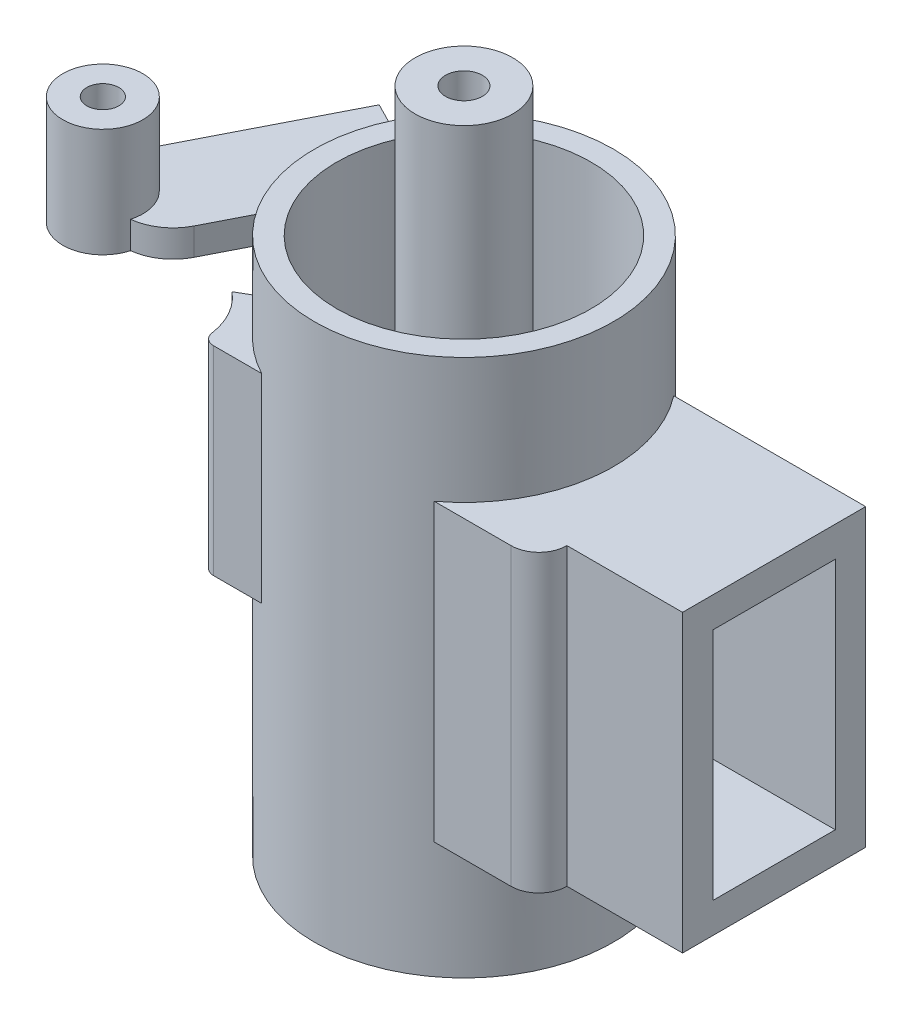
SolidWorks part; units mm, degrees
ref_plane "Front Plane" through (0, 0, 0) normal (0, 0, 1) x (1, 0, 0)
ref_plane "Top Plane" through (0, 0, 0) normal (0, 1, 0) x (1, 0, 0)
ref_plane "Right Plane" through (0, 0, 0) normal (1, 0, 0) x (0, 0, -1)
sketch "Sketch1" plane through (0, 0, 0) normal (0, 1, 0) x (1, 0, 0)
  circle A0 centre (0, 0) radius 9.35
  circle A1 centre (0, 0) radius 7.95
  dimension "D1" = 18.7
  dimension "D2" = 15.9
extrude "Boss-Extrude1" add sketch "Sketch1" along normal blind 31.6
ref_plane "Plane1" through (0, -3.3, 0) normal (0, 1, 0) x (1, 0, 0)
sketch "Sketch2" plane through (0, -3.3, 0) normal (0, 1, 0) x (1, 0, 0)
  circle A0 centre (0, 0) radius 3.05
  circle A1 centre (0, 0) radius 1.15
  dimension "D1" = 6.1
  dimension "D2" = 2.3
extrude "Boss-Extrude2" add sketch "Sketch2" along normal blind 45 separate body
ref_plane "Plane2" through (0, 7.3, 0) normal (0, 1, 0) x (1, 0, 0)
sketch "Sketch4" plane through (0, 7.3, 0) normal (0, 1, 0) x (1, 0, 0)
  line L0 (7.3924, 5.725) -> (19.3924, 5.725)
  line L1 (19.3924, 5.725) -> (19.3924, -5.725)
  line L2 (19.3924, -5.725) -> (11.6224, -5.725)
  line L4 (10.4167, -7.475) -> (5.6167, -7.475)
  circle A0 centre (0, 0) radius 9.35 construction
  arc A1 (10.4167, -7.475) -> (12.1667, -5.725) centre (10.4167, -5.725) ccw
  arc A2 (5.6167, -7.475) -> (7.3924, 5.725) centre (0, 0) ccw
  dimension "D6" = 1.75
  dimension "D1" = 5.725
  dimension "D2" = 5.725
  dimension "D3" = 12
  dimension "D4" = 4.8
  dimension "D5" = 7.77
extrude "Boss-Extrude3" add sketch "Sketch4" along normal blind 18.45
sketch "Sketch5" plane through (19.3924, 0, 0) normal (1, 0, 0) x (0, 0, -1)
  line L0 (3.825, 23.85) -> (-3.825, 23.85)
  line L1 (-3.825, 23.85) -> (-3.825, 9.2)
  line L2 (-3.825, 9.2) -> (3.825, 9.2)
  line L3 (3.825, 9.2) -> (3.825, 23.85)
  line L12 (5.725, 25.75) -> (-7.475, 25.75) construction
  line L13 (5.725, 7.3) -> (-5.725, 7.3) construction
  line L14 (-5.725, 25.75) -> (-5.725, 7.3) construction
  line L15 (5.725, 25.75) -> (5.725, 7.3) construction
  dimension "D1" = 1.9
  dimension "D2" = 1.9
  dimension "D3" = 1.9
  dimension "D4" = 1.9
extrude "Cut-Extrude1" cut sketch "Sketch5" against normal blind 15
ref_plane "Plane3" through (0, 16, 0) normal (0, 1, 0) x (1, 0, 0)
sketch "Sketch6" plane through (0, 16, 0) normal (0, 1, 0) x (1, 0, 0)
  circle A0 centre (0, 0) radius 3.05 construction
  circle A1 centre (0, 0) radius 7.95 construction
  circle A2 centre (0, 0) radius 3.05
  circle A3 centre (0, 0) radius 7.95
extrude "Boss-Extrude4" add sketch "Sketch6" along normal blind 0.2
sketch "Sketch7" plane through (0, 16, 0) normal (0, 1, 0) x (1, 0, 0)
  line L0 (6.9694, 3.825) -> (1.0694, 3.825)
  line L1 (1.0694, 3.825) -> (1.0694, 2.8564)
  line L2 (6.9694, -3.825) -> (1.0694, -3.825)
  line L3 (1.0694, -3.825) -> (1.0694, -2.8564)
  circle A0 centre (0, 0) radius 3.05 construction
  arc A2 (1.0694, -2.8564) -> (1.0694, 2.8564) centre (0, 0) ccw
  arc A4 (6.9694, -3.825) -> (6.9694, 3.825) centre (0, 0) ccw construction
  arc A5 (6.9694, -3.825) -> (6.9694, 3.825) centre (0, 0) ccw
  dimension "D1" = 5.9
extrude "Cut-Extrude4" cut sketch "Sketch7" along normal up to surface (0.2 mm away) up to face at (0, 16.2, 0)
ref_plane "Plane5" through (0, 20.6, 0) normal (0, 1, 0) x (1, 0, 0)
sketch "Sketch8" plane through (0, 20.6, 0) normal (0, 1, 0) x (1, 0, 0)
  line L0 (-4.4, -8.25) -> (-7.4035, -8.25)
  line L1 (-9.7502, -4.75) -> (-8.4512, -4)
  circle A0 centre (0, 0) radius 9.35 construction
  arc A1 (-8.1459, -7.6064) -> (-9.7502, -4.75) centre (-12.6367, -8.25) ccw
  arc A2 (-8.4512, -4) -> (-4.4, -8.25) centre (0, 0) ccw
  arc A3 (-7.4035, -8.25) -> (-8.1459, -7.6064) centre (-7.4035, -7.5) cw
  point P8 (0, -9.35)
  point P17 (-8.1, -8.25)
  dimension "D6" = 0.75
  dimension "D1" = 3.7
  dimension "D2" = 1.5
  dimension "D3" = 1.1
  dimension "D4" = 4.75
  dimension "D5" = 4
extrude "Boss-Extrude5" add sketch "Sketch8" along normal blind 7.45
sketch "Sketch9" plane through (0, 31.6, 0) normal (0, 1, 0) x (1, 0, 0)
  line L0 (-8.3283, 4.25) -> (-10.8223, 5.5227)
  line L1 (-10.8223, 5.5227) -> (-17.0292, -6.6402)
  line L2 (-17.0292, -6.6402) -> (-14.0898, -8.1402)
  line L3 (-10.054, -6.8317) -> (-8.5261, -3.8377)
  circle A0 centre (0, 0) radius 9.35 construction
  arc A1 (-8.3283, 4.25) -> (-8.5261, -3.8377) centre (0, 0) ccw
  arc A2 (-14.0898, -8.1402) -> (-10.054, -6.8317) centre (-12.7262, -5.4681) ccw
  point P3 (-8.3283, 4.25)
  point P4 (-8.3283, -4.25)
  point P12 (-11.4176, -9.5039)
  dimension "D5" = 3
  dimension "D1" = 8.5
  dimension "D2" = 2.8
  dimension "D4" = 6.3
extrude "Boss-Extrude6" add sketch "Sketch9" against normal blind 1.7 separate body
sketch "Sketch10" plane through (0, 31.6, 0) normal (0, 1, 0) x (1, 0, 0)
  line L1 (-10.8223, 5.5227) -> (-17.0292, -6.6402) construction
  line L2 (-17.0292, -6.6402) -> (-14.0898, -8.1402) construction
  circle A0 centre (-14.8024, -7.7766) radius 2.5
  circle A2 centre (-14.8024, -7.7766) radius 1
  dimension "D1" = 5
  dimension "D2" = 2
extrude "Boss-Extrude7" add sketch "Sketch10" along normal blind 6 and the other way up to surface
sketch "Sketch11" plane through (0, 31.6, 0) normal (0, 1, 0) x (1, 0, 0)
  line L0 (-15.6931, -7.3221) -> (-14.0898, -8.1402)
  line L1 (-15.6931, -7.3221) -> (-14.0898, -8.1402)
  circle A0 centre (-14.8024, -7.7766) radius 1 construction
  arc A1 (-15.6931, -7.3221) -> (-13.9086, -8.2252) centre (-14.8024, -7.7766) ccw
  arc A2 (-14.0898, -8.1402) -> (-13.9086, -8.2252) centre (-12.7262, -5.4681) ccw
  arc A3 (-13.9086, -8.2252) -> (-15.6931, -7.3221) centre (-14.8024, -7.7766) ccw
  arc A4 (-14.0898, -8.1402) -> (-13.9086, -8.2252) centre (-12.7262, -5.4681) ccw
  dimension "D1" = 0
extrude "Boss-Extrude8" add sketch "Sketch11" against normal up to surface (1.7 mm away) up to face at (-11.4784, 29.9, 3.1366)
sketch "Sketch12" plane through (0, 20.6, 0) normal (0, -1, 0) x (1, 0, 0)
  line L2 (-4.4, 8.25) -> (-7.4035, 8.25)
  line L3 (-9.7502, 4.75) -> (-8.4512, 4)
  line L4 (-4.4, 8.25) -> (-7.4035, 8.25)
  line L5 (-9.7502, 4.75) -> (-8.4512, 4)
  arc A3 (-4.4, 8.25) -> (-8.4512, 4) centre (0, 0) ccw
  arc A4 (-7.4035, 8.25) -> (-8.1459, 7.6064) centre (-7.4035, 7.5) ccw
  arc A5 (-9.7502, 4.75) -> (-8.1459, 7.6064) centre (-12.6367, 8.25) ccw
  arc A6 (-4.4, 8.25) -> (-8.4512, 4) centre (0, 0) ccw
  arc A7 (-7.4035, 8.25) -> (-8.1459, 7.6064) centre (-7.4035, 7.5) ccw
  arc A8 (-9.7502, 4.75) -> (-8.1459, 7.6064) centre (-12.6367, 8.25) ccw
  dimension "D1" = 0
extrude "Boss-Extrude9" add sketch "Sketch12" along normal blind 5
sketch "Sketch13" plane through (0, 31.6, 0) normal (0, 1, 0) x (1, 0, 0)
  circle A0 centre (0, 0) radius 7.95 construction
  circle A1 centre (0, 0) radius 9.35
  circle A2 centre (0, 0) radius 9.35
  circle A3 centre (0, 0) radius 7.95
  dimension "D1" = 0
extrude "Boss-Extrude12" add sketch "Sketch13" along normal blind 2 contours A2 | A3
sketch "Sketch14" plane through (0, 31.6, 0) normal (0, 1, 0) x (1, 0, 0)
  line L3 (-10.054, -6.8317) -> (-8.5261, -3.8377)
  line L4 (-8.3283, 4.25) -> (-10.8223, 5.5227)
  line L5 (-10.8223, 5.5227) -> (-17.0292, -6.6402)
  line L6 (-10.054, -6.8317) -> (-8.5261, -3.8377)
  line L7 (-8.3283, 4.25) -> (-10.8223, 5.5227)
  line L8 (-10.8223, 5.5227) -> (-17.0292, -6.6402)
  circle A1 centre (-14.8024, -7.7766) radius 2.5
  arc A2 (-17.0292, -6.6402) -> (-12.3947, -8.4497) centre (-14.8024, -7.7766) ccw
  arc A3 (-8.3283, 4.25) -> (-8.5261, -3.8377) centre (0, 0) ccw
  arc A4 (-12.3947, -8.4497) -> (-17.0292, -6.6402) centre (-14.8024, -7.7766) ccw
  arc A5 (-12.3947, -8.4497) -> (-10.054, -6.8317) centre (-12.7262, -5.4681) ccw
  arc A6 (-8.3283, 4.25) -> (-8.5261, -3.8377) centre (0, 0) ccw
  arc A8 (-12.3947, -8.4497) -> (-10.054, -6.8317) centre (-12.7262, -5.4681) ccw
  dimension "D1" = 0
  dimension "D2" = 0
extrude "Boss-Extrude13" add sketch "Sketch14" against normal up to surface (1.7 mm away) up to face at (-11.4784, 29.9, 3.1366)
sketch "Sketch15" plane through (0, 29.9, 0) normal (0, -1, 0) x (1, 0, 0)
  line L3 (-17.0292, 6.6402) -> (-10.8223, -5.5227)
  line L4 (-10.8223, -5.5227) -> (-8.3283, -4.25)
  line L5 (-8.5261, 3.8377) -> (-10.054, 6.8317)
  line L6 (-17.0292, 6.6402) -> (-10.8223, -5.5227)
  line L7 (-10.8223, -5.5227) -> (-8.3283, -4.25)
  line L8 (-8.5261, 3.8377) -> (-10.054, 6.8317)
  arc A3 (-10.054, 6.8317) -> (-12.3947, 8.4497) centre (-12.7262, 5.4681) ccw
  arc A4 (-12.3947, 8.4497) -> (-17.0292, 6.6402) centre (-14.8024, 7.7766) ccw
  arc A5 (-8.5261, 3.8377) -> (-8.3283, -4.25) centre (0, 0) ccw
  arc A6 (-10.054, 6.8317) -> (-12.3947, 8.4497) centre (-12.7262, 5.4681) ccw
  arc A7 (-12.3947, 8.4497) -> (-17.0292, 6.6402) centre (-14.8024, 7.7766) ccw
  arc A8 (-8.5261, 3.8377) -> (-8.3283, -4.25) centre (0, 0) ccw
  dimension "D1" = 0
extrude "Cut-Extrude5" cut sketch "Sketch15" against normal blind 0.9
sketch "Sketch17" plane through (0, 31.6, 0) normal (0, 1, 0) x (1, 0, 0)
  line L3 (-10.054, -6.8317) -> (-8.5261, -3.8377)
  line L4 (-8.3283, 4.25) -> (-10.8223, 5.5227)
  line L5 (-10.8223, 5.5227) -> (-17.0292, -6.6402)
  line L6 (-10.054, -6.8317) -> (-8.5261, -3.8377)
  line L7 (-8.3283, 4.25) -> (-10.8223, 5.5227)
  line L8 (-10.8223, 5.5227) -> (-17.0292, -6.6402)
  circle A0 centre (-14.8024, -7.7766) radius 2.5 construction
  arc A1 (-17.0292, -6.6402) -> (-12.3947, -8.4497) centre (-14.8024, -7.7766) ccw
  arc A3 (-8.3283, 4.25) -> (-8.5261, -3.8377) centre (0, 0) ccw
  arc A4 (-12.3947, -8.4497) -> (-17.0292, -6.6402) centre (-14.8024, -7.7766) ccw
  arc A5 (-12.3947, -8.4497) -> (-10.054, -6.8317) centre (-12.7262, -5.4681) ccw
  arc A6 (-8.3283, 4.25) -> (-8.5261, -3.8377) centre (0, 0) ccw
  arc A8 (-12.3947, -8.4497) -> (-10.054, -6.8317) centre (-12.7262, -5.4681) ccw
  dimension "D1" = 0
extrude "Boss-Extrude14" add sketch "Sketch17" along normal blind 0.9
